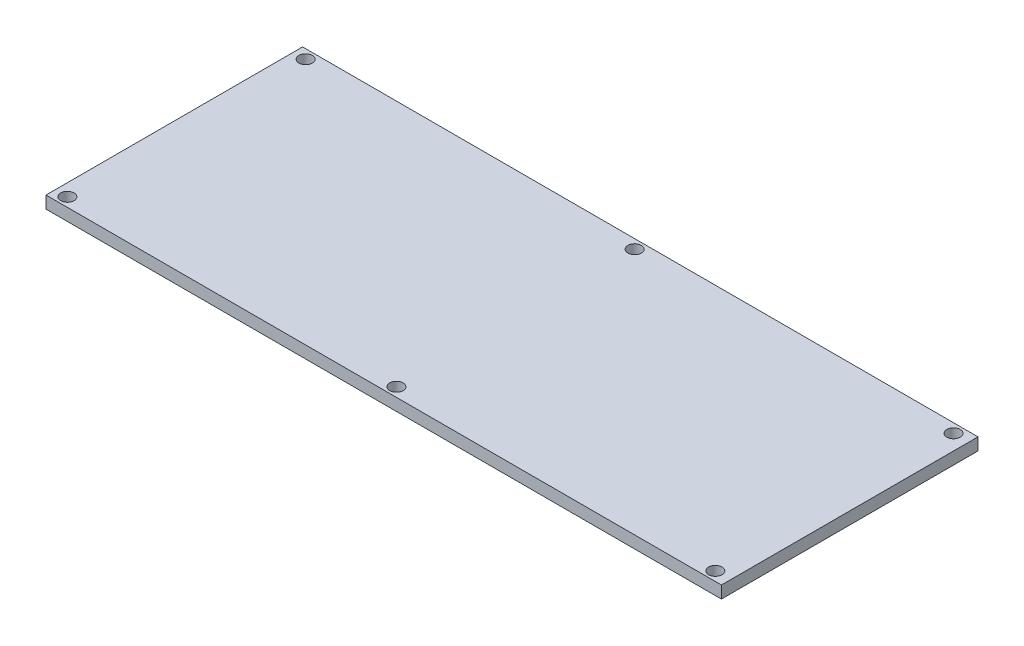
SolidWorks part; units mm, degrees
material "1060 Alloy"
ref_plane "Front Plane" through (0, 0, 0) normal (0, 0, 1) x (1, 0, 0)
ref_plane "Top Plane" through (0, 0, 0) normal (0, 1, 0) x (1, 0, 0)
ref_plane "Right Plane" through (0, 0, 0) normal (1, 0, 0) x (0, 0, -1)
sketch "Sketch1" plane through (0, 0, 0) normal (0, 1, 0) x (1, 0, 0)
  line L1 (-55.28, -21) -> (55.28, -21)
  line L2 (-55.28, -21) -> (-55.28, 21)
  line L3 (-55.28, 21) -> (55.28, 21)
  line L4 (55.28, -21) -> (55.28, 21)
  line L5 (-55.28, -21) -> (55.28, 21) construction
  line L6 (-55.28, 21) -> (55.28, -21) construction
  point P0 (0, 0)
  dimension "D1" = 110.56
  dimension "D2" = 42
extrude "Boss-Extrude1" add sketch "Sketch1" along normal blind 2
hole_wizard "Ø2.2 (2.2) Diameter Hole1" positions "Sketch10" profile "Sketch11" hole size "Ø2.2" standard "ANSI Metric" end condition up to next
sketch "Sketch10" plane through (0, 0, 0) normal (0, -1, 0) x (-1, 0, 0)
  line L0 (55.28, -21) -> (-55.28, -21) construction
  line L1 (-55.28, 21) -> (55.28, 21) construction
  line L2 (55.28, 21) -> (55.28, -21) construction
  point P0 (53.28, -19.5)
  point P3 (53.28, 19.5)
  point P6 (-52.78, 19.5)
  point P9 (-0.5795, 19.5)
  point P23 (-0.5795, -19.5)
  point P25 (-52.78, -19.5)
  point P27 (0, 0)
  point P28 (0, 0)
  point P29 (0, 0)
  point P30 (0, 0)
  dimension "D1" = 1.5
  dimension "D2" = 1.5
  dimension "D3" = 2
sketch "Sketch11" plane through (-53.28, 0, 19.5) normal (1, 0, 0) x (0, 0, -1)
  line L0 (0, 0) -> (0, 2)
  line L1 (0, 2) -> (1.1, 2)
  line L2 (1.1, 2) -> (1.1, 0)
  line L5 (1.1, 0) -> (0, 0)
  line L11 (0, -6.35) -> (0, 107.95) construction
  dimension "Thru Hole Dia." = 2.2
  dimension "Thru Hole Depth" = 2
